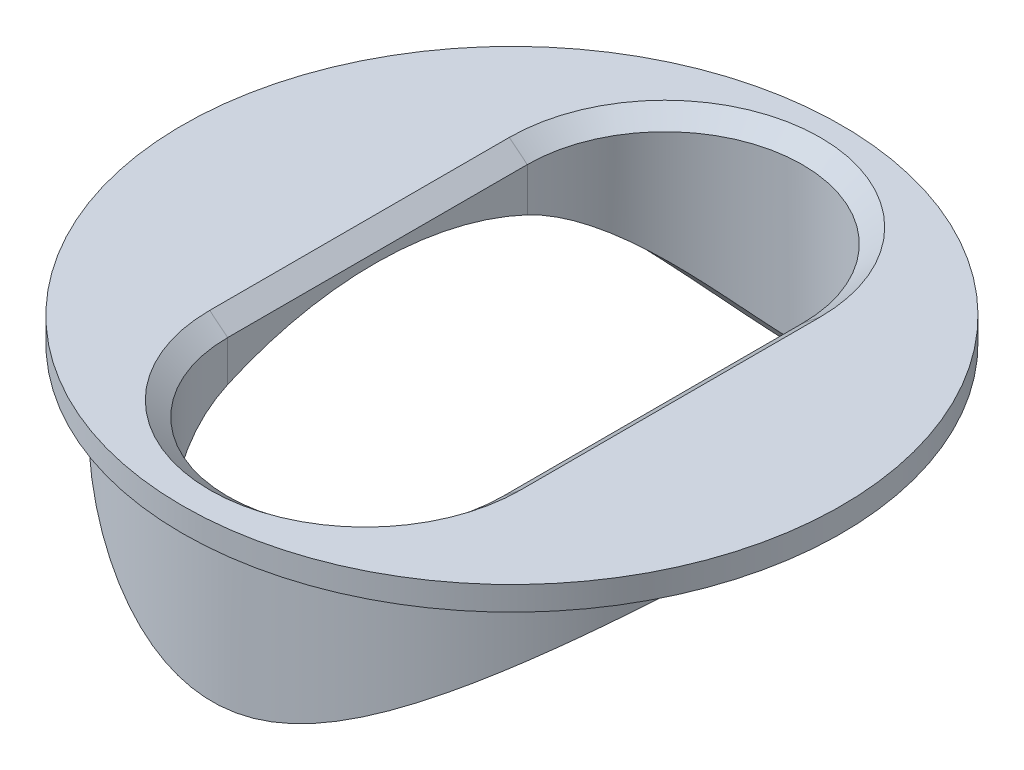
SolidWorks part; units mm, degrees
ref_plane "Front Plane" through (0, 0, 0) normal (0, 0, 1) x (1, 0, 0)
ref_plane "Top Plane" through (0, 0, 0) normal (0, 1, 0) x (1, 0, 0)
ref_plane "Right Plane" through (0, 0, 0) normal (1, 0, 0) x (0, 0, -1)
sketch "Sketch1" plane through (0, 0, 0) normal (0, 1, 0) x (1, 0, 0)
  circle A0 centre (0, 0) radius 5
extrude "Boss-Extrude1" add sketch "Sketch1" along normal blind 5
sketch "Sketch2" plane through (0, 5, 0) normal (0, 1, 0) x (1, 0, 0)
  circle A0 centre (0, 0) radius 5.5
extrude "Boss-Extrude2" add sketch "Sketch2" along normal blind 0.4
sketch "Sketch4" plane through (0, 5.4, 0) normal (0, 1, 0) x (1, 0, 0)
  line L0 (0, 2.5514) -> (0, -2.4486) construction
  line L1 (2.2953, 2.5514) -> (2.2953, -2.4486)
  line L2 (-2.2953, 2.5514) -> (-2.2953, -2.4486)
  arc A0 (2.2953, 2.5514) -> (-2.2953, 2.5514) centre (0, 2.5514) ccw
  arc A1 (-2.2953, -2.4486) -> (2.2953, -2.4486) centre (0, -2.4486) ccw
  point P3 (0, 0.0514)
  dimension "D1" = 2.5
  dimension "D2" = 2.5
extrude "Cut-Extrude1" cut sketch "Sketch4" against normal through all
sketch "Sketch5" plane through (0, 0, 0) normal (1, 0, 0) x (0, 0, -1)
  circle A0 centre (0, -1) radius 6
extrude "Cut-Extrude2" cut sketch "Sketch5" against normal through all and the other way through all
sketch "Sketch6" plane through (0, 5.4, 0) normal (0, 1, 0) x (-1, 0, 0)
  circle A0 centre (0, 0) radius 5
chamfer "Chamfer4" distance 0.3 angle 39 4 edges at (0, 5.4, -4.8466) (-2.2953, 5.4, -0.0514) (2.2953, 5.4, -0.0514) (0, 5.4, 4.7439)
